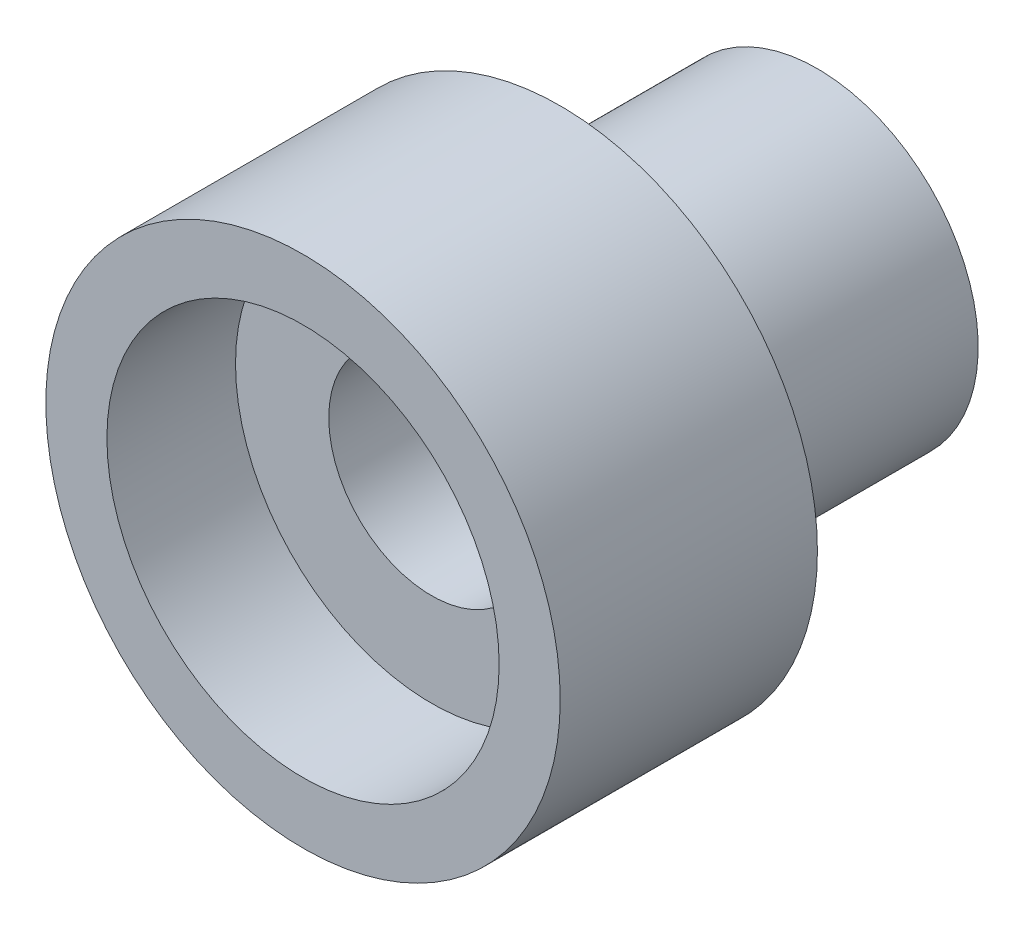
SolidWorks part; units mm, degrees
ref_plane "前视基准面" through (0, 0, 0) normal (0, 0, 1) x (1, 0, 0)
ref_plane "上视基准面" through (0, 0, 0) normal (0, 1, 0) x (1, 0, 0)
ref_plane "右视基准面" through (0, 0, 0) normal (1, 0, 0) x (0, 0, -1)
sketch "草图1" plane through (0, 0, 0) normal (0, 0, 1) x (1, 0, 0)
  circle A0 centre (0, 0) radius 4
extrude "凸台-拉伸1" add sketch "草图1" along normal blind 4
sketch "草图4" plane through (0, 0, 0) normal (0, 0, -1) x (-1, 0, 0)
  circle A0 centre (0, 0) radius 2.5
extrude "凸台-拉伸2" add sketch "草图4" along normal blind 4
sketch "草图2" plane through (0, 0, 0) normal (0, 0, -1) x (-1, 0, 0)
  circle A0 centre (0, 0) radius 1.6
extrude "切除-拉伸1" cut sketch "草图2" along direction (0, 0, -1) on the side against the normal blind 3 and the other way up to surface (4 mm away)
sketch "草图3" plane through (0, 0, 4) normal (0, 0, 1) x (1, 0, 0)
  circle A0 centre (0, 0) radius 3.05
extrude "切除-拉伸2" cut sketch "草图3" against normal blind 2
